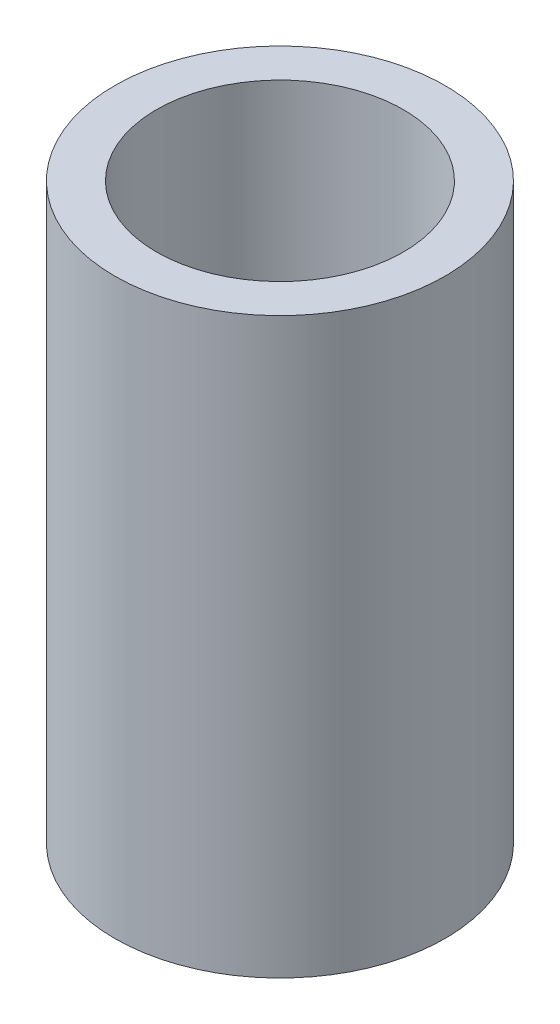
SolidWorks part; units mm, degrees
ref_plane "Front Plane" through (0, 0, 0) normal (0, 0, 1) x (1, 0, 0)
ref_plane "Top Plane" through (0, 0, 0) normal (0, 1, 0) x (1, 0, 0)
ref_plane "Right Plane" through (0, 0, 0) normal (1, 0, 0) x (0, 0, -1)
sketch "Sketch1" plane through (0, 0, 0) normal (0, 1, 0) x (1, 0, 0)
  circle A0 centre (0, 0) radius 2.0765
  circle A1 centre (0, 0) radius 2.7781
  dimension "D1" = 5.5562
  dimension "D2" = 4.1529
extrude "Boss-Extrude1" add sketch "Sketch1" along normal blind 9.652
sketch "Sketch2" plane through (0, 9.652, 0) normal (0, 1, 0) x (1, 0, 0)
  circle A0 centre (0, 0) radius 3.392
extrude "Boss-Extrude2" [suppressed] add sketch "Sketch2" along normal blind 2.286
